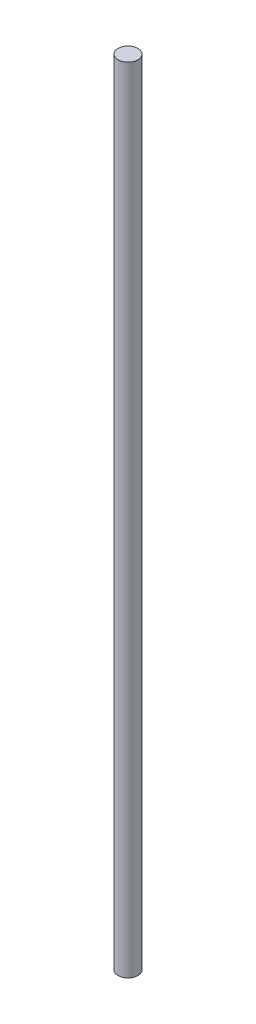
SolidWorks part; units mm, degrees
material "1060 Alloy"
ref_plane "Front Plane" through (0, 0, 0) normal (0, 0, 1) x (1, 0, 0)
ref_plane "Top Plane" through (0, 0, 0) normal (0, 1, 0) x (1, 0, 0)
ref_plane "Right Plane" through (0, 0, 0) normal (1, 0, 0) x (0, 0, -1)
sketch "Sketch1" plane through (0, 0, 0) normal (0, 1, 0) x (1, 0, 0)
  circle A0 centre (0, 0) radius 3.175
  dimension "D1" = 6.35
extrude "Boss-Extrude1" add sketch "Sketch1" along normal mid plane 254
